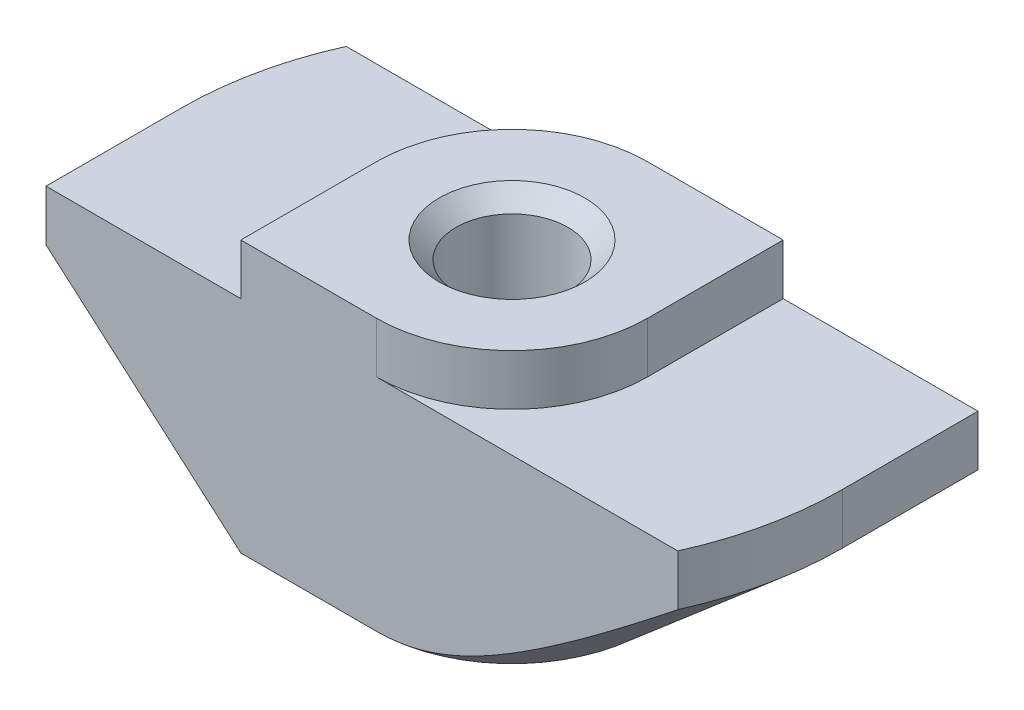
SolidWorks part; units mm, degrees
material "Сталь 20  ГОСТ 1050-2013"
ref_plane "Спереди" through (0, 0, 0) normal (0, 0, 1) x (1, 0, 0)
ref_plane "Сверху" through (0, 0, 0) normal (0, 1, 0) x (1, 0, 0)
ref_plane "Справа" through (0, 0, 0) normal (1, 0, 0) x (0, 0, -1)
sketch "Эскиз1" plane through (0, 0, 0) normal (0, 0, 1) x (1, 0, 0)
  line L0 (4, 0) -> (-4, 0)
  line L1 (-4, 0) -> (-4, -1.5)
  line L2 (-4, -1.5) -> (-9.75, -1.5)
  line L3 (-9.75, -1.5) -> (-9.75, -8)
  line L4 (-9.75, -8) -> (9.75, -8)
  line L5 (0, -8) -> (0, 0) construction
  line L6 (9.75, -1.5) -> (9.75, -8)
  line L7 (4, -1.5) -> (9.75, -1.5)
  line L8 (4, 0) -> (4, -1.5)
  dimension "D1" = 8
  dimension "D2" = 19.5
  dimension "D3" = 8
  dimension "D4" = 1.5
extrude "Бобышка-Вытянуть1" add sketch "Эскиз1" along normal mid plane 8
hole_wizard "Отверстие обработанное метчиком M43" positions "Эскиз2" profile "Эскиз3" tap size "M4" standard "ISO" end condition up to next
sketch "Эскиз2" plane through (0, 0, 0) normal (0, 1, 0) x (1, 0, 0)
  point P0 (0, 0)
sketch "Эскиз3" plane through (0, 0, 0) normal (1, 0, 0) x (0, 0, 1)
  line L0 (0, 0) -> (0, 8)
  line L1 (0, 8) -> (2.15, 8)
  line L2 (1.65, 7.5) -> (1.65, 0.5)
  line L3 (1.65, 0.5) -> (2.15, 0)
  line L5 (2.15, 0) -> (0, 0)
  line L6 (-1.65, 0.5) -> (-2.15, 0) construction
  line L7 (2.15, 8) -> (1.65, 7.5)
  line L8 (-2.15, 8) -> (-1.65, 7.5) construction
  line L11 (0, -6.35) -> (0, 107.95) construction
  dimension "Диаметр проходного сверла" = 3.3
  dimension "Глубина проходного сверла" = 8
  dimension "Диаметр передней зенковки" = 4.3
  dimension "Угол передней зенковки" = 90
  dimension "Диаметр задней зенковки" = 4.3
  dimension "Угол задней зенковки" = 90
cosmetic thread "Отверстие резьбы1" parameters "D2"=4
sketch "Эскиз4" plane through (0, 0, 0) normal (0, 1, 0) x (1, 0, 0)
  line L0 (-4, 4) -> (-4, 0)
  line L1 (-4, -4) -> (-4, 4) construction
  line L2 (4, 4) -> (-4, 4) construction
  line L3 (0, 4) -> (-4, 4)
  line L4 (0, -4) -> (4, -4)
  line L5 (4, -4) -> (-4, -4) construction
  line L6 (4, -4) -> (4, 0)
  line L7 (4, -4) -> (4, 4) construction
  arc A0 (-4, 0) -> (0, 4) centre (0, 0) cw
  arc A1 (4, 0) -> (0, -4) centre (0, 0) cw
extrude "Вырез-Вытянуть1" cut sketch "Эскиз4" against normal up to surface (1.5 mm away) up to face at (-6.875, -1.5, 0)
sketch "Эскиз5" plane through (0, -1.5, 0) normal (0, 1, 0) x (1, 0, 0)
  line L0 (-9.75, 0) -> (-9.75, 4)
  line L1 (-9.75, -4) -> (-9.75, 4) construction
  line L2 (-9.75, 4) -> (-8.8917, 4)
  line L3 (0, 4) -> (-9.75, 4) construction
  line L4 (9.75, 0) -> (9.75, -4)
  line L5 (9.75, -4) -> (9.75, 4) construction
  line L6 (9.75, -4) -> (8.8917, -4)
  line L7 (9.75, -4) -> (0, -4) construction
  arc A0 (-8.8917, 4) -> (-9.75, 0) centre (0, 0) ccw
  arc A2 (9.75, 0) -> (8.8917, -4) centre (0, 0) cw
  point P19 (0, 0)
extrude "Вырез-Вытянуть2" cut sketch "Эскиз5" against normal through all
sketch "Эскиз6" plane through (0, 0, 4) normal (0, 0, 1) x (1, 0, 0)
  line L0 (-9.75, -3) -> (-9.75, -8)
  line L1 (-9.75, -1.5) -> (-9.75, -8) construction
  line L2 (-9.75, -8) -> (-4, -8)
  line L3 (-9.75, -8) -> (8.8917, -8) construction
  line L4 (-4, -8) -> (-9.75, -3)
  line L5 (-4, -1.5) -> (-9.75, -1.5) construction
  line L6 (-4, 0) -> (-4, -1.5) construction
  point P10 (0, 0)
  dimension "D1" = 1.5
sketch "Эскиз7" plane through (0, -8, 0) normal (0, -1, 0) x (1, 0, 0)
  line L0 (0, 9.75) -> (-9.75, 9.75)
  line L1 (-9.75, 9.75) -> (-9.75, 0)
  line L2 (0, -9.75) -> (9.75, -9.75)
  line L3 (9.75, -9.75) -> (9.75, 0)
  arc A0 (-9.75, 0) -> (0, -9.75) centre (0, 0) ccw
  arc A1 (9.75, 0) -> (0, 9.75) centre (0, 0) ccw
sweep "Вырез-По траектории1" cut profiles "Эскиз6" path "Эскиз7"
